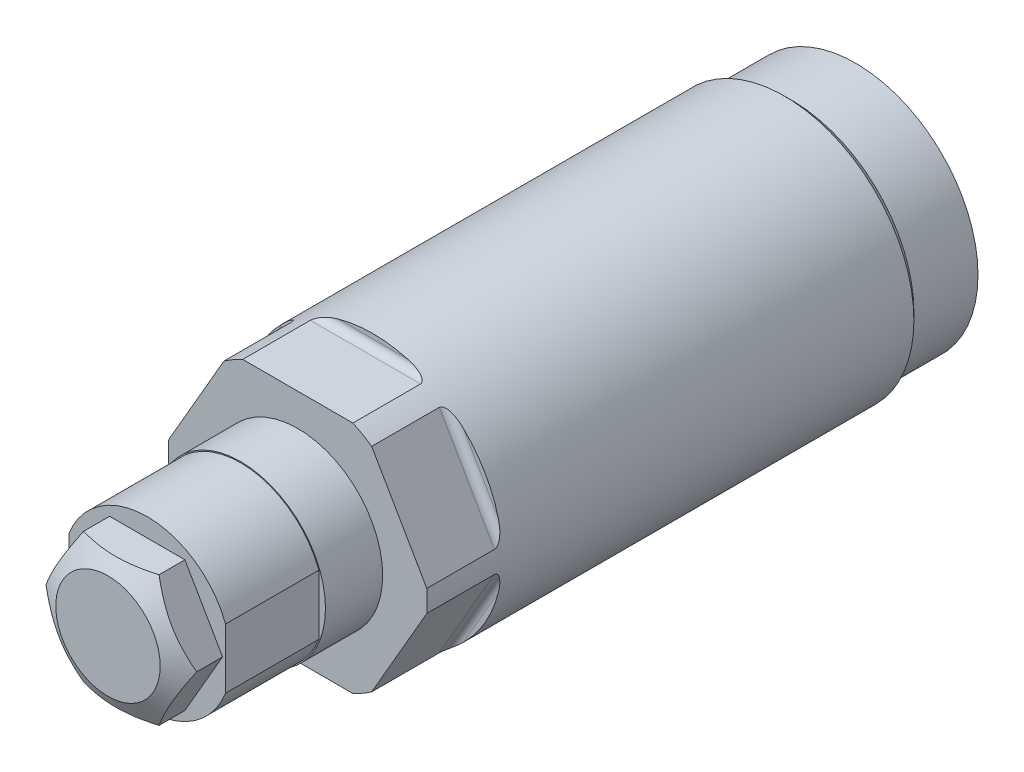
SolidWorks part; units mm, degrees
material "Alloy Steel"
ref_plane "Front Plane" through (0, 0, 0) normal (0, 0, 1) x (1, 0, 0)
ref_plane "Top Plane" through (0, 0, 0) normal (0, 1, 0) x (1, 0, 0)
ref_plane "Right Plane" through (0, 0, 0) normal (1, 0, 0) x (0, 0, -1)
ref_plane "Plane1" through (0, 0, 0) normal (0, 0, 1) x (1, 0, 0)
ref_plane "Plane2" through (0, 0, 0) normal (0, 0, 1) x (1, 0, 0)
sketch "Sketch1" plane through (0, 0, 0) normal (0, 0, 1) x (1, 0, 0)
  circle A0 centre (0, 0) radius 15.748
  dimension "D1" = 31.496
extrude "Extrude1" add sketch "Sketch1" along normal blind 67.8688
ref_plane "Plane3" through (0, 0, 0) normal (1, 0, 0) x (0, 0, 1)
sketch "Sketch2" plane through (0, 0, 0) normal (1, 0, 0) x (0, 0, 1)
  line L0 (58.7248, 15.748) -> (58.7248, 15.1638)
  line L1 (59.6392, 14.2494) -> (67.8688, 14.2494)
  line L2 (45.5676, 0) -> (55.626, 0) construction
  line L3 (58.7248, 15.748) -> (67.8688, 15.748)
  line L4 (67.8688, 15.748) -> (67.8688, 14.2494)
  arc A0 (58.7248, 15.1638) -> (59.6392, 14.2494) centre (59.6392, 15.1638) ccw
  dimension "D3" = 0.9144
  dimension "D1" = 9.144
  dimension "D2" = 28.4988
extrude "Cut-Extrude1" cut sketch "Sketch2" against normal mid plane 37.7952
ref_plane "Plane13" through (0, 0, 0) normal (1, 0, 0) x (0, 0, 1)
sketch "Sketch10" plane through (0, 0, 0) normal (1, 0, 0) x (0, 0, 1)
  line L0 (0, 14.8717) -> (7.7978, 14.8717)
  line L1 (7.7978, 14.8717) -> (8.6741, 15.748)
  line L2 (8.6741, 15.748) -> (0, 15.748)
  line L3 (0, 15.748) -> (0, 14.8717)
  line L4 (-0.4337, 0) -> (9.1078, 0) construction
  line L5 (58.7248, 15.748) -> (0, 15.748) construction
  line L6 (0, 15.748) -> (0, -15.748) construction
  dimension "D1" = 29.7434
  dimension "D2" = 7.7978
  dimension "D3" = 45
revolve "Cut-Revolve1" cut sketch "Sketch10" angle 360 about L4
ref_plane "Plane14" through (0, 0, 0) normal (1, 0, 0) x (0, 0, -1)
sketch "Sketch11" plane through (0, 0, 0) normal (1, 0, 0) x (0, 0, -1)
  line L0 (-67.8688, 0) -> (-86.1822, 0)
  line L1 (-86.1822, 0) -> (-86.1822, 10.3251)
  line L2 (-86.1822, 10.3251) -> (-67.8688, 10.3251)
  line L3 (-67.8688, 10.3251) -> (-67.8688, 0)
  line L4 (-71.0641, 0) -> (-39.4872, 0) construction
  line L5 (-67.8688, 15.748) -> (-67.8688, -14.2494) construction
  dimension "D1" = 20.6502
  dimension "D2" = 18.3134
revolve "Revolve1" add sketch "Sketch11" angle 360 about L4
ref_plane "Plane15" through (-4.5466, 0, 70.3072) normal (0, 1, 0) x (-1, 0, 0)
sketch "S2D0011" plane through (-4.5466, 0, 70.3072) normal (0, 1, 0) x (-1, 0, 0)
  line L0 (0, 15.875) -> (0, 9.525)
  line L1 (0, 9.525) -> (-4.5466, 9.525)
  line L2 (0, 15.875) -> (-4.5466, 15.875)
  line L3 (-4.5466, 15.875) -> (-4.5466, 9.525)
  line L4 (-4.5466, -22.2401) -> (-4.5466, 0.3175) construction
  line L5 (5.7785, 15.875) -> (-14.8717, 15.875) construction
  dimension "D1" = 6.35
  dimension "D2" = 9.0932
revolve "Cut-Revolve2" cut sketch "S2D0011" angle 360 about L4
ref_plane "Plane16" through (0, 0, 58.9534) normal (0, 0, -1) x (0, 1, 0)
sketch "Sketch14" plane through (0, 0, 86.1822) normal (0, 0, -1) x (0, 1, 0)
  line L0 (-3.9852, 9.525) -> (3.9852, 9.525)
  line L1 (-3.9852, -9.525) -> (3.9852, -9.525)
  line L2 (-11.3576, 0) -> (11.3576, 0) construction
  arc A0 (3.9852, 9.525) -> (-3.9852, 9.525) centre (0, 0) ccw
  arc A1 (-3.9852, -9.525) -> (3.9852, -9.525) centre (0, 0) ccw
  dimension "D2" = 10.3251
  dimension "D1" = 19.05
extrude "Cut-Extrude10" cut sketch "Sketch14" along normal blind 11.3538
sketch "Sketch15" plane through (0, 0, 86.1822) normal (0, 0, 1) x (1, 0, 0)
  line L0 (-4.5827, 7.9375) -> (4.5827, 7.9375)
  line L1 (4.5827, 7.9375) -> (9.1654, 0)
  line L2 (9.1654, 0) -> (4.5827, -7.9375)
  line L3 (4.5827, -7.9375) -> (-4.5827, -7.9375)
  line L4 (-4.5827, -7.9375) -> (-9.1654, 0)
  line L5 (-9.1654, 0) -> (-4.5827, 7.9375)
  line L6 (-10.082, 0) -> (10.082, 0) construction
  dimension "D1" = 15.875
extrude "Extrude2" add sketch "Sketch15" along normal blind 4.7752
ref_plane "Plane18" through (0, 0, 0) normal (0, 1, 0) x (1, 0, 0)
sketch "Sketch16" plane through (0, 0, 0) normal (0, 1, 0) x (1, 0, 0)
  line L0 (6.35, -90.9574) -> (9.1654, -89.3319)
  line L1 (0, -75.1637) -> (0, -58.4454) construction
  line L2 (6.35, -90.9574) -> (9.1654, -90.9574)
  line L3 (9.1654, -90.9574) -> (9.1654, -89.3319)
  dimension "D1" = 12.7
  dimension "D2" = 30
revolve "Cut-Revolve3" cut sketch "Sketch16" angle 360 about L1
pattern_circular "CirPattern2" count 6 over 360 about axis through (0, 0, 0) along (0, 0, 1) of "Cut-Extrude1"
sketch "Sketch18" plane through (0, 0, 0) normal (1, 0, 0) x (0, 0, -1)
  line L0 (0, 0) -> (-90.9574, 0) construction
  line L1 (-90.9574, 6.35) -> (-90.9574, -6.35) construction
  line L2 (-74.8284, 10.3251) -> (-86.1822, 10.3251)
  line L3 (-67.8688, 10.3251) -> (-86.1822, 10.3251) construction
  line L4 (-86.1822, 10.3251) -> (-86.1822, 10.1981)
  line L5 (-86.1822, 10.3251) -> (-86.1822, 3.9852) construction
  line L6 (-86.1822, 10.1981) -> (-74.8284, 10.1981)
  line L7 (-74.8284, 10.1981) -> (-74.8284, 10.3251)
  dimension "D1" = 11.3538
  dimension "D2" = 20.3962
revolve "Cut-Revolve4" cut sketch "Sketch18" angle 360 about L0
